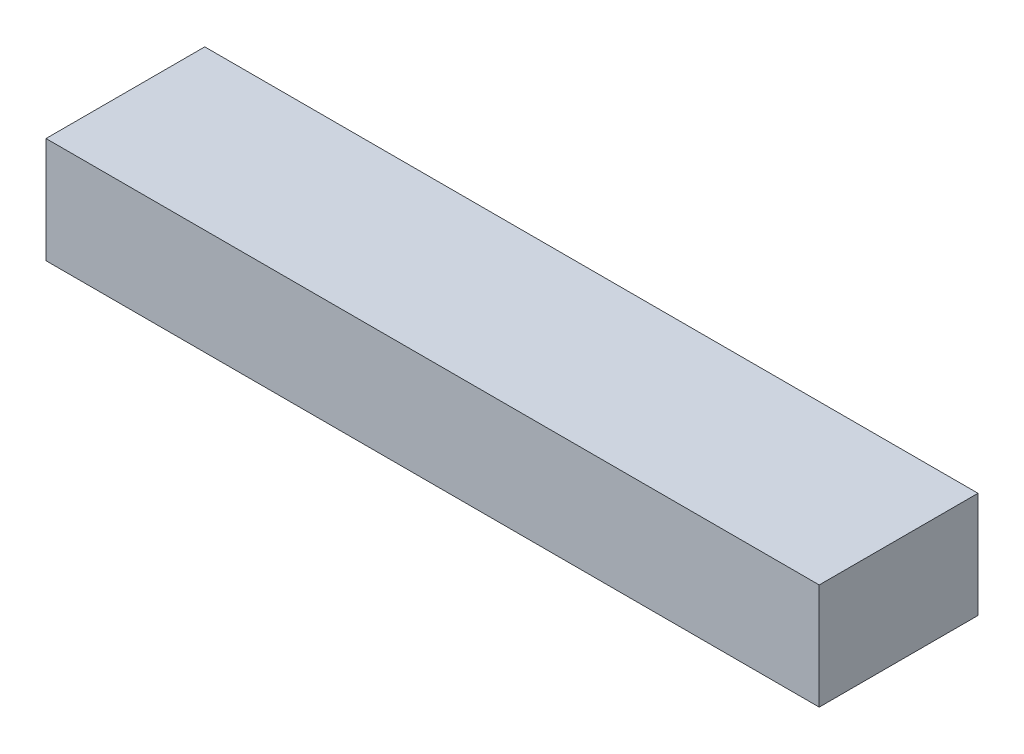
SolidWorks part; units mm, degrees
ref_plane "前视基准面" through (0, 0, 0) normal (0, 0, 1) x (1, 0, 0)
ref_plane "上视基准面" through (0, 0, 0) normal (0, 1, 0) x (1, 0, 0)
ref_plane "右视基准面" through (0, 0, 0) normal (1, 0, 0) x (0, 0, -1)
sketch "草图1" plane through (0, 0, 0) normal (0, 1, 0) x (1, 0, 0)
  line L1 (-34.2078, 24.1629) -> (38.8422, 24.1629)
  line L2 (-34.2078, 24.1629) -> (-34.2078, 39.1629)
  line L3 (-34.2078, 39.1629) -> (38.8422, 39.1629)
  line L4 (38.8422, 24.1629) -> (38.8422, 39.1629)
  dimension "D1" = 73.05
  dimension "D2" = 15
extrude "凸台-拉伸1" add sketch "草图1" along normal blind 10
